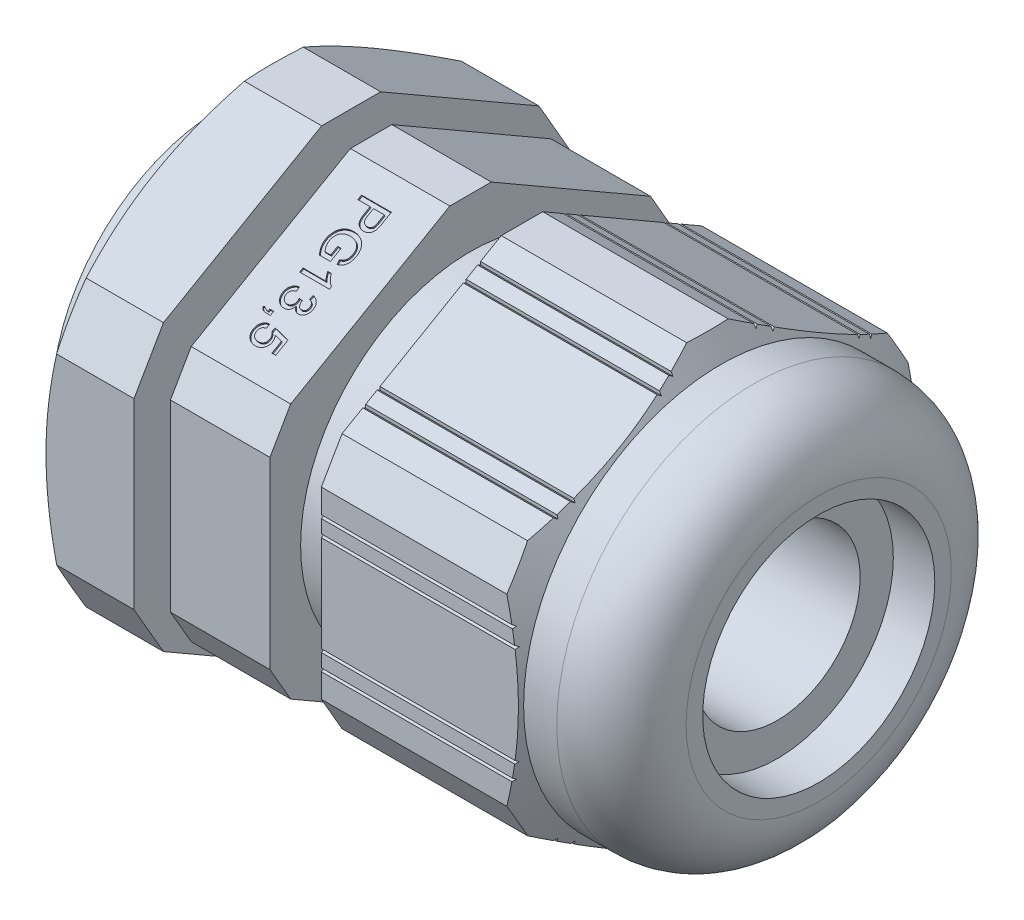
SolidWorks part; units mm, degrees
material "Náilon 6/10"
ref_plane "Plano frontal" through (0, 0, 0) normal (0, 0, 1) x (1, 0, 0)
ref_plane "Plano superior" through (0, 0, 0) normal (0, 1, 0) x (1, 0, 0)
ref_plane "Plano direito" through (0, 0, 0) normal (1, 0, 0) x (0, 0, -1)
sketch "Esboço1" plane through (0, 0, 0) normal (1, 0, 0) x (0, 0, -1)
  line L1 (-12.1, 6.9859) -> (-12.1, -6.9859)
  line L2 (-12.1, -6.9859) -> (0, -13.9719)
  line L3 (0, -13.9719) -> (12.1, -6.9859)
  line L4 (12.1, -6.9859) -> (12.1, 6.9859)
  line L5 (12.1, 6.9859) -> (0, 13.9719)
  line L6 (0, 13.9719) -> (-12.1, 6.9859)
  circle A0 centre (0, 0) radius 12.1 construction
  circle A1 centre (0, 0) radius 7
  dimension "D2" = 14
  dimension "D1" = 24.2
extrude "Ressalto-extrusão1" add sketch "Esboço1" along normal mid plane 36
sketch "Esboço2" plane through (0, 0, 0) normal (0, 0, 1) x (1, 0, 0)
  line L0 (18, -7) -> (18, 7) construction
  line L1 (18, -7) -> (18, 7) construction
  line L2 (18, 7) -> (18, 8) construction
  line L3 (18, 13.9719) -> (18, 6.9859) construction
  line L5 (14.1, 11.9) -> (12.1, 11.9)
  line L6 (0, 0) -> (18, 0) construction
  line L7 (12.1, 11.9) -> (10.9038, 13.9719)
  line L8 (18, 13.9719) -> (-18, 13.9719) construction
  line L9 (10.9038, 13.9719) -> (18, 13.9719)
  line L10 (0.1, 13.9719) -> (0.1, 10.25)
  line L11 (0.1, 10.25) -> (-3, 10.25)
  line L12 (-3, 10.25) -> (-3, 13.9719)
  line L13 (-3, 13.9719) -> (0.1, 13.9719)
  line L14 (-9, 13.9719) -> (-9, 10.25)
  line L15 (18, 13.9719) -> (18, 8)
  line L16 (-9, 10.25) -> (-18, 10.25)
  line L17 (-18, 13.9719) -> (-18, 6.9859) construction
  line L18 (-18, 10.25) -> (-18, 13.9719)
  line L19 (-18, 13.9719) -> (-9, 13.9719)
  arc A0 (18, 8) -> (14.1, 11.9) centre (14.1, 8) ccw
  dimension "D1" = 2
  dimension "D2" = 1
  dimension "D3" = 23.8
  dimension "D4" = 60
  dimension "D5" = 12
  dimension "D6" = 6
  dimension "D7" = 27
  dimension "D8" = 20.5
revolve "Corte-Revolução1" cut sketch "Esboço2" angle 360 about L6
sketch "Esboço3" plane through (-9, 0, 0) normal (-1, 0, 0) x (0, 0, 1)
  line L6 (-7.6499, 13.25) -> (-15.2998, 0)
  line L7 (-15.2998, 0) -> (-7.6499, -13.25)
  line L8 (-7.6499, -13.25) -> (7.6499, -13.25)
  line L9 (7.6499, -13.25) -> (15.2998, 0)
  line L10 (15.2998, 0) -> (7.6499, 13.25)
  line L11 (7.6499, 13.25) -> (-7.6499, 13.25)
  circle A0 centre (0, 0) radius 13.25 construction
  dimension "D1" = 26.5
extrude "Corte-extrusão1" cut sketch "Esboço3" against normal blind 36 flip side to cut
sketch "Esboço5" plane through (0.1, 0, 0) normal (-1, 0, 0) x (0, 0, 1)
  line L0 (0, 0) -> (12.1, 0) construction
  line L1 (12.1, 4.1) -> (11.9268, 4)
  line L2 (11.9268, 4) -> (12.1, 3.9)
  line L3 (12.1, 3.9) -> (12.1, 4.1)
  line L4 (12.1, 3.1) -> (11.9268, 3)
  line L5 (11.9268, 3) -> (12.1, 2.9)
  line L6 (12.1, 2.9) -> (12.1, 3.1)
  line L7 (12.1, -2.9) -> (12.1, -3.1)
  line L8 (11.9268, -3) -> (12.1, -2.9)
  line L9 (12.1, -3.1) -> (11.9268, -3)
  line L10 (12.1, -3.9) -> (12.1, -4.1)
  line L11 (11.9268, -4) -> (12.1, -3.9)
  line L12 (12.1, -4.1) -> (11.9268, -4)
  line L13 (12.1, -5.5422) -> (12.1, 5.5422) construction
  point P2 (12.1, 4)
  point P17 (12.1, 3)
  dimension "D1" = 0.2
  dimension "D2" = 4
  dimension "D3" = 1
extrude "Corte-extrusão3" cut sketch "Esboço5" against normal up to next
pattern_circular "PadrãoCircular2" count 6 over 360 about axis through (0, 0, 0) along (1, 0, 0) of "Corte-extrusão3"
ref_plane "Plano1" through (-10.2, 0, 0) normal (-1, 0, 0) x (0, 0, 1)
sketch "Esboço6" plane through (-10.2, 0, 0) normal (-1, 0, 0) x (0, 0, 1)
  line L0 (-12.1, 5.5422) -> (-12.1, -5.5422) construction
  line L1 (-1.7781, 14.1) -> (-11.3219, 8.5899)
  line L2 (-13.1, 5.5101) -> (-13.1, -5.5101)
  line L3 (-11.3219, -8.5899) -> (-1.7781, -14.1)
  line L4 (1.7781, -14.1) -> (11.3219, -8.5899)
  line L5 (13.1, -5.5101) -> (13.1, 5.5101)
  line L6 (11.3219, 8.5899) -> (1.7781, 14.1)
  line L8 (-13.1, -5.5101) -> (-11.3219, -8.5899)
  line L9 (-1.7781, -14.1) -> (1.7781, -14.1)
  line L10 (11.3219, -8.5899) -> (13.1, -5.5101)
  line L11 (13.1, 5.5101) -> (11.3219, 8.5899)
  line L12 (1.7781, 14.1) -> (-1.7781, 14.1)
  line L13 (-11.3219, 8.5899) -> (-13.1, 5.5101)
  circle A0 centre (0, 0) radius 13.1 construction
  circle A1 centre (0, 0) radius 10.25 construction
  circle A2 centre (0, 0) radius 10.25
  circle A3 centre (0, 0) radius 14.1 construction
  dimension "D2" = 28.2
  dimension "D1" = 1
extrude "PORCA" add sketch "Esboço6" along normal blind 6
sketch "Esboço7" plane through (0, 0, 0) normal (0, 0, 1) x (1, 0, 0)
  line L0 (-16.2, 11.9) -> (-13.3132, 16.9)
  line L1 (-16.2, 8.5899) -> (-16.2, 14.1) construction
  line L2 (-13.3132, 16.9) -> (-16.2, 16.9)
  line L3 (-16.2, 16.9) -> (-16.2, 11.9)
  line L4 (14.1, 11.9) -> (12.1, 11.9) construction
  line L5 (0, 0) -> (-18, 0) construction
  line L6 (-18, 10.25) -> (-18, -10.25) construction
  dimension "D1" = 30
  dimension "D2" = 5
revolve "Corte-Revolução2" cut sketch "Esboço7" angle 360 about L5
ref_plane "Plano2" through (15.5, 0, 0) normal (1, 0, 0) x (0, 0, -1)
sketch "Esboço8" plane through (15.5, 0, 0) normal (1, 0, 0) x (0, 0, -1)
  circle A0 centre (0, 0) radius 7 construction
  circle A1 centre (0, 0) radius 7
  circle A2 centre (0, 0) radius 5
  dimension "D1" = 10
extrude "BORRACHA" add sketch "Esboço8" against normal blind 10 separate body
sketch "Esboço9" plane through (0, 10.4789, 6.05) normal (0, 0.866, 0.5) x (1, 0, 0)
  line L0 (-7, 5.5422) -> (-7, -5.5422) construction
  line L1 (-9, 5.5422) -> (-3, 5.5422) construction
  line L2 (-3, -5.5422) -> (-9, -5.5422) construction
  line L3 (-9, -5.5422) -> (-9, 5.5422) construction
  text T0 "PG13,5" font "Arial" height in points 7
  dimension "D1" = 2
extrude "PG13,5" cut sketch "Esboço9" against normal blind 0.1
